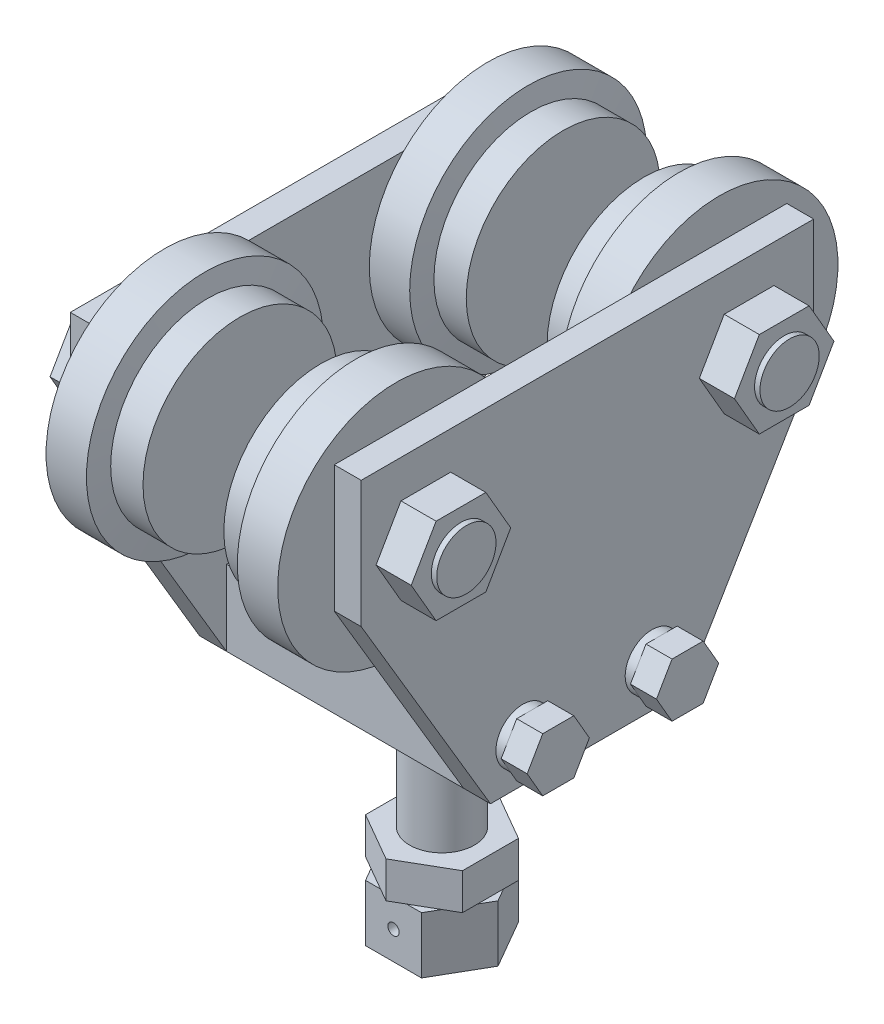
SolidWorks part; units mm, degrees
ref_plane "Front" through (0, 0, 0) normal (0, 0, 1) x (1, 0, 0)
ref_plane "Top" through (0, 0, 0) normal (0, 1, 0) x (1, 0, 0)
ref_plane "Right" through (0, 0, 0) normal (1, 0, 0) x (0, 0, -1)
ref_plane "Z PLANE" through (0, 0, 0) normal (0, 0, 1) x (1, 0, 0)
ref_plane "YOKE BOTTOM" through (0, 0, 0) normal (0, 1, 0) x (-1, 0, 0)
ref_plane "X PLANE" through (0, 0, 0) normal (1, 0, 0) x (0, 0, -1)
sketch "YOKE CROSS SECTION" plane through (0, 0, 0) normal (1, 0, 0) x (0, 0, -1)
  line L0 (0, 0) -> (0, 57.0916) construction
  line L1 (0, 84.8167) -> (0, -84.8167) construction
  line L2 (-57.15, 0) -> (57.15, 0)
  line L3 (69.1602, 0) -> (-69.1602, 0) construction
  line L4 (57.15, 0) -> (57.15, 44.45)
  line L5 (-57.15, 0) -> (-57.15, 44.45)
  line L6 (57.15, 44.45) -> (-57.15, 44.45)
  point P12 (0, 44.45)
  dimension "D1" = 44.45
  dimension "D2" = 114.3
ref_plane "1/2 YOKE LENGTH (A)" through (69.85, 0, 0) normal (1, 0, 0) x (0, 0, -1)
ref_plane "WHEEL LOCATION" through (0, 0, 95.25) normal (0, 0, 1) x (1, 0, 0)
extrude "YOKE" add sketch "YOKE CROSS SECTION" along normal up to surface (69.85 mm away) up to plane "1/2 YOKE LENGTH (A)"
sketch "SIDEPLATE PROFILE" plane through (69.85, 0, 0) normal (1, 0, 0) x (0, 0, -1)
  line L0 (-133.35, 203.2) -> (-133.35, 128.5178)
  line L1 (0, 84.8167) -> (0, -84.8167) construction
  line L2 (133.35, 203.2) -> (133.35, 128.5178)
  line L3 (0, 0) -> (-57.15, 0)
  line L4 (-133.35, 128.5178) -> (-57.15, 0)
  line L5 (133.35, 128.5178) -> (57.15, 0)
  line L6 (0, 0) -> (57.15, 0)
  line L7 (-133.35, 203.2) -> (133.35, 203.2)
  line L8 (69.1602, 0) -> (-69.1602, 0) construction
  dimension "D1" = 57.15
  dimension "D2" = 76.2
  dimension "D3" = 76.2
  dimension "D4" = 57.15
  dimension "D5" = 76.2
  dimension "D6" = 76.2
  dimension "D7" = 266.7
  dimension "D8" = 128.5178
  dimension "D9" = 128.5178
  dimension "D10" = 203.2
ref_plane "WHEEL HEIGHT" through (0, 155.575, 0) normal (0, 1, 0) x (-1, 0, 0)
ref_plane "YOKE SCREW LOCATION Z" through (0, 0, 38.1) normal (0, 0, 1) x (1, 0, 0)
ref_plane "YOKE SCREW LOCATION Y" through (0, 25.4, 0) normal (0, 1, 0) x (-1, 0, 0)
extrude "SIDEPLATE" add sketch "SIDEPLATE PROFILE" along normal blind 15.875
sketch "WHEEL PIN NUT PROFILE" plane through (85.725, 0, 0) normal (1, 0, 0) x (0, 0, -1)
  line L0 (-95.25, 84.8167) -> (-95.25, -84.8167) construction
  line L1 (-65.9206, 155.575) -> (-80.5853, 180.975)
  line L2 (-80.5853, 180.975) -> (-109.9147, 180.975)
  line L3 (-109.9147, 180.975) -> (-124.5794, 155.575)
  line L4 (-124.5794, 155.575) -> (-109.9147, 130.175)
  line L5 (-109.9147, 130.175) -> (-80.5853, 130.175)
  line L6 (-80.5853, 130.175) -> (-65.9206, 155.575)
  line L7 (69.1602, 155.575) -> (-69.1602, 155.575) construction
  circle A0 centre (-95.25, 155.575) radius 13.4938 construction
  dimension "D1" = 50.8
extrude "WHEEL PIN NUT" add sketch "WHEEL PIN NUT PROFILE" along normal blind 20.701
sketch "WHEEL PIN PROJECTION PROFILE" plane through (106.426, 0, 0) normal (1, 0, 0) x (0, 0, -1)
  line L0 (-95.25, 84.8167) -> (-95.25, -84.8167) construction
  line L3 (69.1602, 155.575) -> (-69.1602, 155.575) construction
  circle A0 centre (-95.25, 155.575) radius 17.4625
  dimension "D1" = 34.925
extrude "WHEEL PIN PROJECTION" add sketch "WHEEL PIN PROJECTION PROFILE" along normal blind 3.175
sketch "LOCKNUTS PROFILE" plane through (85.725, 0, 0) normal (1, 0, 0) x (0, 0, -1)
  line L0 (-38.1, 84.8167) -> (-38.1, -84.8167) construction
  line L1 (50, 25.4) -> (-50, 25.4) construction
  circle A0 centre (-38.1, 25.4) radius 15.875
  dimension "D1" = 31.75
extrude "LOCKNUTS" add sketch "LOCKNUTS PROFILE" along normal blind 5.5626
sketch "SCREWS PROFILE" plane through (91.2876, 0, 0) normal (1, 0, 0) x (0, 0, -1)
  line L0 (50, 25.4) -> (-50, 25.4) construction
  line L1 (-19.7691, 25.4) -> (-28.9346, 41.275)
  line L2 (-28.9346, 41.275) -> (-47.2654, 41.275)
  line L3 (-47.2654, 41.275) -> (-56.4309, 25.4)
  line L4 (-56.4309, 25.4) -> (-47.2654, 9.525)
  line L5 (-47.2654, 9.525) -> (-28.9346, 9.525)
  line L6 (-28.9346, 9.525) -> (-19.7691, 25.4)
  line L7 (-38.1, 84.8167) -> (-38.1, -84.8167) construction
  circle A0 centre (-38.1, 25.4) radius 15.875 construction
  dimension "D1" = 31.75
extrude "SCREWS" add sketch "SCREWS PROFILE" along normal blind 15.3416
sketch "PROFILE" plane through (0, 44.45, 0) normal (0, 1, 0) x (-1, 0, 0)
  line L0 (84.8167, 0) -> (-84.8167, 0) construction
  line L1 (0, 83.2389) -> (0, -83.2389) construction
  circle A0 centre (0, 0) radius 28.575
  dimension "D1" = 57.15
extrude "KING BOLT HEAD" add sketch "PROFILE" along normal blind 31.75
mirror "Mirror1" about plane through (0, 0, 0) normal (0, 0, 1) of "WHEEL PIN PROJECTION", "WHEEL PIN NUT"
mirror "Mirror YOKE SCREWS" about plane through (0, 0, 0) normal (0, 0, 1) of "SCREWS", "LOCKNUTS"
mirror "Mirror SIDE 1" about plane through (0, 0, 0) normal (1, 0, 0) of bodies 112
ref_plane "TOP OF NUT" through (0, -83.0521, 0) normal (0, 1, 0) x (-1, 0, 0)
sketch "DIA." plane through (0, 0, 0) normal (0, -1, 0) x (1, 0, 0)
  line L0 (84.8167, 0) -> (-84.8167, 0) construction
  line L1 (0, -83.2389) -> (0, 83.2389) construction
  circle A0 centre (0, 0) radius 19.05
  dimension "D1" = 38.1
extrude "KING BOLT" add sketch "DIA." along normal up to surface (83.0521 mm away) up to plane "TOP OF NUT"
sketch "KING BOLT JAN NUT PROFILE" plane through (0, -83.0521, 0) normal (0, -1, 0) x (1, 0, 0)
  line L0 (84.8167, 0) -> (-84.8167, 0) construction
  line L1 (0, -32.9956) -> (28.575, -16.4978)
  line L2 (28.575, -16.4978) -> (28.575, 16.4978)
  line L3 (28.575, 16.4978) -> (0, 32.9956)
  line L4 (0, 32.9956) -> (-28.575, 16.4978)
  line L5 (-28.575, 16.4978) -> (-28.575, -16.4978)
  line L6 (-28.575, -16.4978) -> (0, -32.9956)
  line L7 (0, -83.2389) -> (0, 83.2389) construction
  circle A0 centre (0, 0) radius 28.575 construction
  dimension "D1" = 57.15
extrude "KING BOLT JAM NUT" add sketch "KING BOLT JAN NUT PROFILE" along normal blind 21.4312
sketch "KING BOLT NUT PROFILE" plane through (0, -104.4834, 0) normal (0, -1, 0) x (1, 0, 0)
  line L1 (32.9956, 0) -> (16.4978, 28.575)
  line L2 (16.4978, 28.575) -> (-16.4978, 28.575)
  line L3 (-16.4978, 28.575) -> (-32.9956, 0)
  line L4 (-32.9956, 0) -> (-16.4978, -28.575)
  line L5 (-16.4978, -28.575) -> (16.4978, -28.575)
  line L6 (16.4978, -28.575) -> (32.9956, 0)
  line L10 (0, -83.2389) -> (0, 83.2389) construction
  line L11 (84.8167, 0) -> (-84.8167, 0) construction
  circle A0 centre (0, 0) radius 28.575 construction
  dimension "D1" = 57.15
extrude "KING BOLT NUT" add sketch "KING BOLT NUT PROFILE" along normal blind 33.3375
sketch "Sketch5" plane through (0, -137.8209, 0) normal (0, -1, 0) x (1, 0, 0)
  circle A0 centre (0, 0) radius 19.05 construction
  circle A1 centre (0, 0) radius 19.05
extrude "EXTENDED KING BOLT" add sketch "Sketch5" along normal blind 6.35
chamfer "Chamfer1" distance 2.3812 angle 45 1 edges at (0, -144.1709, -19.05)
ref_plane "MOUNTING REF PLANE" through (0, -34.925, 0) normal (0, 1, 0) x (-1, 0, 0)
sketch "Sketch11" plane through (0, 0, -28.575) normal (0, 0, -1) x (-1, 0, 0)
  line L1 (16.4978, -137.8209) -> (-16.4978, -137.8209) construction
  line L2 (0, 83.2389) -> (0, -83.2389) construction
  circle A0 centre (0, -121.1521) radius 3.3401
  point P4 (0, -137.8209)
  dimension "D1" = 6.6802
  dimension "D2" = 16.6687
extrude "COTTER PIN HOLE" cut sketch "Sketch11" against normal up to next
sketch "Sketch12" plane through (0, 0, 95.25) normal (0, 0, 1) x (1, 0, 0)
  line L0 (23.8125, 155.575) -> (23.8125, 212.725)
  line L1 (68.2625, 179.3875) -> (68.2625, 225.425)
  line L2 (69.85, 155.575) -> (69.85, 179.3875)
  line L3 (23.8125, 155.575) -> (69.85, 155.575)
  line L4 (69.85, 179.3875) -> (68.2625, 179.3875)
  line L5 (68.2625, 225.425) -> (44.45, 225.425)
  line L6 (42.8625, 212.725) -> (44.45, 225.425)
  line L7 (42.8625, 212.725) -> (23.8125, 212.725)
  line L8 (69.1602, 155.575) -> (-69.1602, 155.575) construction
  line L9 (69.85, -75.0522) -> (69.85, 75.0522) construction
  dimension "D1" = 1.5875
  dimension "D2" = 46.0375
  dimension "D3" = 1.5875
  dimension "D4" = 25.4
  dimension "D5" = 26.9875
  dimension "D6" = 46.0375
  dimension "D7" = 23.8125
  dimension "D8" = 69.85
  dimension "D9" = 69.85
  dimension "D10" = 57.15
revolve "WHEEL" add sketch "Sketch12" angle 360 about axis through (109.601, 155.575, 95.25) along (-1, 0, 0)
mirror "Mirror2" about plane through (0, 0, 0) normal (0, 0, 1) of "WHEEL"
mirror "Mirror3" about plane through (0, 0, 0) normal (1, 0, 0) of "Mirror2", "WHEEL"
sketch "Sketch13" plane through (0, 0, 0) normal (0, -1, 0) x (1, 0, 0)
  circle A0 centre (0, 0) radius 25.4
  circle A1 centre (0, 0) radius 30.1625
  dimension "D1" = 50.8
  dimension "D2" = 60.325
extrude "SPACER" [suppressed] add sketch "Sketch13" along normal blind 12.7
ref_plane "TREAD OF TRACK" through (0, 98.425, 0) normal (0, 1, 0) x (-1, 0, 0)
